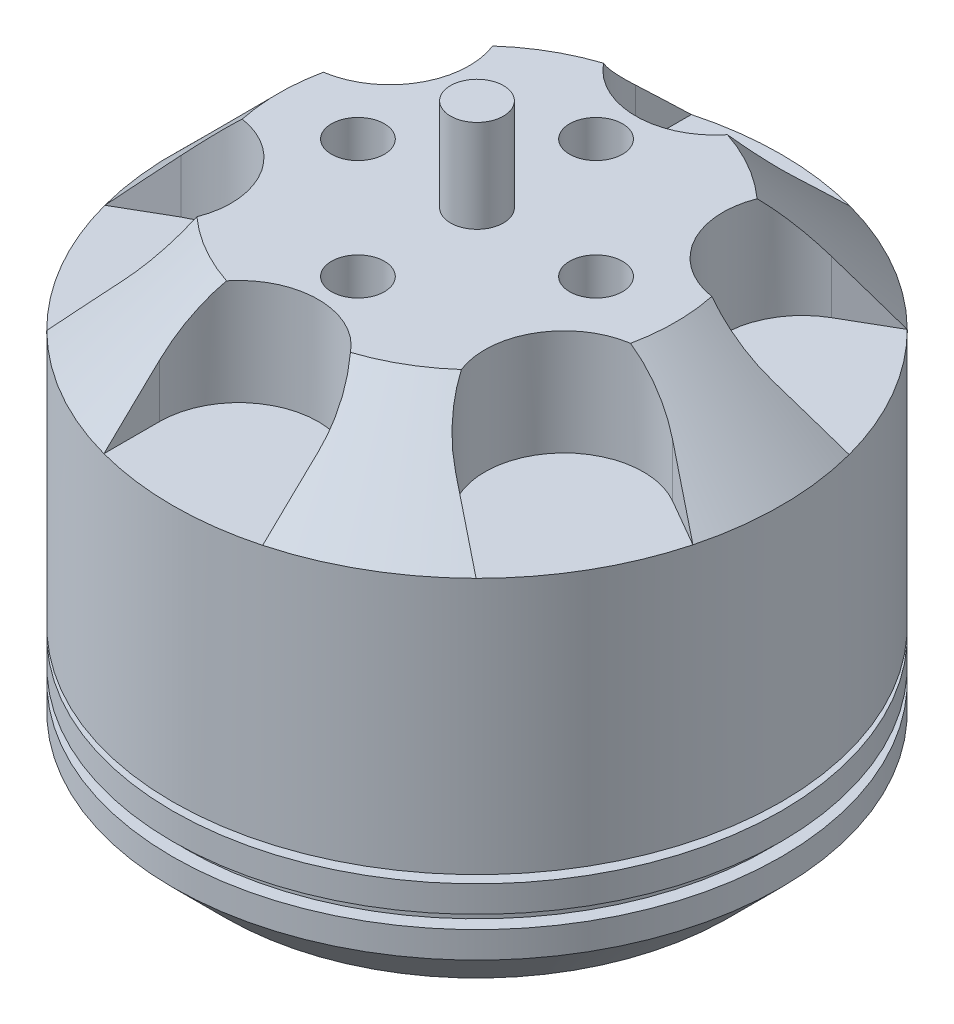
SolidWorks part; units mm, degrees
ref_plane "Front Plane" through (0, 0, 0) normal (0, 0, 1) x (1, 0, 0)
ref_plane "Top Plane" through (0, 0, 0) normal (0, 1, 0) x (1, 0, 0)
ref_plane "Right Plane" through (0, 0, 0) normal (1, 0, 0) x (0, 0, -1)
sketch "Sketch2" plane through (0, 0, 0) normal (0, 0, 1) x (1, 0, 0)
  line L0 (0, 23.8) -> (0, 0)
  line L1 (0, 0) -> (1, 0)
  line L2 (1, 0) -> (1, 1.8)
  line L3 (1, 1.8) -> (9.5, 1.8)
  line L4 (9.5, 1.8) -> (11.5, 3.8)
  line L5 (11.5, 3.8) -> (11.5, 4.8)
  line L6 (11.5, 16.3) -> (7.5, 20.3)
  line L7 (7.5, 20.3) -> (1, 20.3)
  line L8 (1, 20.3) -> (1, 23.8)
  line L9 (1, 23.8) -> (0, 23.8)
  line L10 (2, 19.3) -> (7.0858, 19.3)
  line L11 (7.0858, 19.3) -> (10.5, 15.8858)
  line L12 (10.5, 15.8858) -> (10.5, 7.7948)
  line L13 (10.5, 7.7948) -> (1, 7.7948)
  line L14 (1, 7.7948) -> (1, 18.3)
  line L15 (1, 18.3) -> (2, 18.3)
  line L16 (2, 18.3) -> (2, 19.3)
  line L17 (11.5, 6.6) -> (9.5, 6.6)
  line L18 (9.5, 6.6) -> (9.5, 6.3)
  line L19 (9.5, 6.3) -> (11.5, 6.3)
  line L20 (11.5, 5.3) -> (11, 5.3)
  line L21 (11, 5.3) -> (11, 4.8)
  line L22 (11, 4.8) -> (11.5, 4.8)
  line L23 (11.5, 5.3) -> (11.5, 6.3)
  line L24 (11.5, 6.6) -> (11.5, 16.3)
  dimension "D1" = 23.8
  dimension "D2" = 1
  dimension "D3" = 1
  dimension "D4" = 1.8
  dimension "D5" = 45
  dimension "D6" = 3.5
  dimension "D7" = 11.5
  dimension "D8" = 45
  dimension "D9" = 2
  dimension "D10" = 1
  dimension "D11" = 1
  dimension "D12" = 1
  dimension "D13" = 1
  dimension "D14" = 1
  dimension "D15" = 1
  dimension "D16" = 4
  dimension "D17" = 2
  dimension "D18" = 0.3
  dimension "D19" = 0.5
  dimension "D20" = 0.5
  dimension "D21" = 1
  dimension "D22" = 1
revolve "Revolve2" add sketch "Sketch2" angle 360 about L0
sketch "Sketch3" plane through (0, 20.3, 0) normal (0, 1, 0) x (1, 0, 0)
  line L0 (0, 0) -> (0, 9) construction
  line L1 (0, 9) -> (13.9452, 9) construction
  line L2 (13.9452, 9) -> (13.9452, 0) construction
  line L3 (13.9452, 0) -> (0, 0) construction
  line L4 (-3, 9) -> (-3, 17.2743)
  line L5 (-3, 17.2743) -> (3, 17.2743)
  line L6 (3, 17.2743) -> (3, 9)
  line L7 (13.46, 11.2352) -> (16.46, 6.0391)
  line L8 (16.46, 6.0391) -> (9.2942, 1.9019)
  line L9 (6.2942, 7.0981) -> (13.46, 11.2352)
  line L10 (16.46, -6.0391) -> (13.46, -11.2352)
  line L11 (13.46, -11.2352) -> (6.2942, -7.0981)
  line L12 (9.2942, -1.9019) -> (16.46, -6.0391)
  line L13 (3, -17.2743) -> (-3, -17.2743)
  line L14 (-3, -17.2743) -> (-3, -9)
  line L15 (3, -9) -> (3, -17.2743)
  line L16 (-13.46, -11.2352) -> (-16.46, -6.0391)
  line L17 (-16.46, -6.0391) -> (-9.2942, -1.9019)
  line L18 (-6.2942, -7.0981) -> (-13.46, -11.2352)
  line L19 (-16.46, 6.0391) -> (-13.46, 11.2352)
  line L20 (-13.46, 11.2352) -> (-6.2942, 7.0981)
  line L21 (-9.2942, 1.9019) -> (-16.46, 6.0391)
  circle A1 centre (0, 4.5) radius 1
  circle A2 centre (0, -4.5) radius 1
  circle A3 centre (4.5, 0) radius 1
  circle A4 centre (-4.5, 0) radius 1
  arc A5 (-3, 9) -> (3, 9) centre (0, 9) ccw
  arc A6 (6.2942, 7.0981) -> (9.2942, 1.9019) centre (7.7942, 4.5) ccw
  arc A7 (9.2942, -1.9019) -> (6.2942, -7.0981) centre (7.7942, -4.5) ccw
  arc A8 (3, -9) -> (-3, -9) centre (0, -9) ccw
  arc A9 (-6.2942, -7.0981) -> (-9.2942, -1.9019) centre (-7.7942, -4.5) ccw
  arc A10 (-9.2942, 1.9019) -> (-6.2942, 7.0981) centre (-7.7942, 4.5) ccw
  point P46 (0, 0)
  dimension "D2" = 2
  dimension "D4" = 6
  dimension "D3" = 9
  dimension "D5" = 6
extrude "Cut-Extrude1" cut sketch "Sketch3" against normal blind 4
sketch "Sketch4" plane through (0, 1.8, 0) normal (0, -1, 0) x (1, 0, 0)
  circle A0 centre (0, 0) radius 8 construction
  circle A1 centre (0, 0) radius 6 construction
  circle A2 centre (0, 6) radius 1
  circle A3 centre (8, 0) radius 1
  circle A4 centre (0, -6) radius 1
  circle A5 centre (-8, 0) radius 1
  dimension "D1" = 16
  dimension "D2" = 12
  dimension "D3" = 2
extrude "Cut-Extrude2" cut sketch "Sketch4" against normal blind 3
